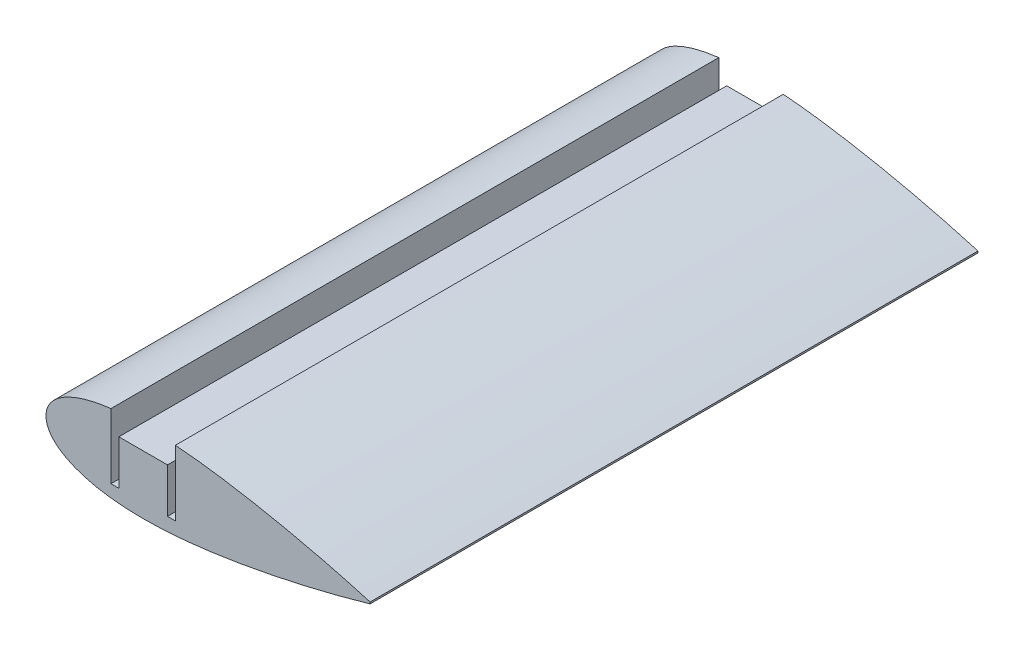
SolidWorks part; units mm, degrees
ref_plane "Спереди" through (0, 0, 0) normal (0, 0, 1) x (1, 0, 0)
ref_plane "Сверху" through (0, 0, 0) normal (0, 1, 0) x (1, 0, 0)
ref_plane "Справа" through (0, 0, 0) normal (1, 0, 0) x (0, 0, -1)
other "Configuration Table"
curve "Curve1"
  spline degree 3 poles (1, 0.0026, 0) (0.9995, 0.0028, 0) (0.9974, 0.0034, 0) (0.9928, 0.0047, 0) (0.9852, 0.0069, 0) (0.9746, 0.01, 0) (0.961, 0.0138, 0) (0.9446, 0.0183, 0) (0.9255, 0.0235, 0) (0.9037, 0.0292, 0) (0.8794, 0.0355, 0) (0.8529, 0.0421, 0) (0.8241, 0.0491, 0) (0.7933, 0.0562, 0) (0.7607, 0.0635, 0) (0.7266, 0.0709, 0) (0.691, 0.0782, 0) (0.6542, 0.0854, 0) (0.6165, 0.0923, 0) (0.5781, 0.0988, 0) (0.5392, 0.1049, 0) (0.5, 0.1104, 0) (0.4609, 0.1152, 0) (0.422, 0.1192, 0) (0.3836, 0.1222, 0) (0.3458, 0.1243, 0) (0.3091, 0.1252, 0) (0.2735, 0.1249, 0) (0.2392, 0.1234, 0) (0.2066, 0.1205, 0) (0.1758, 0.1164, 0) (0.147, 0.111, 0) (0.1203, 0.1043, 0) (0.096, 0.0965, 0) (0.0741, 0.0875, 0) (0.0549, 0.0774, 0) (0.0383, 0.0665, 0) (0.0245, 0.0546, 0) (0.0137, 0.042, 0) (0.0058, 0.0286, 0) (0.001, 0.0145, 0) (-0.0005, 0, 0) (0.001, -0.0145, 0) (0.0058, -0.0286, 0) (0.0137, -0.042, 0) (0.0245, -0.0546, 0) (0.0383, -0.0665, 0) (0.0549, -0.0774, 0) (0.0741, -0.0875, 0) (0.096, -0.0965, 0) (0.1203, -0.1043, 0) (0.147, -0.111, 0) (0.1758, -0.1164, 0) (0.2066, -0.1205, 0) (0.2392, -0.1234, 0) (0.2735, -0.1249, 0) (0.3091, -0.1252, 0) (0.3458, -0.1243, 0) (0.3836, -0.1222, 0) (0.422, -0.1192, 0) (0.4609, -0.1152, 0) (0.5, -0.1104, 0) (0.5392, -0.1049, 0) (0.5781, -0.0988, 0) (0.6165, -0.0923, 0) (0.6542, -0.0854, 0) (0.691, -0.0782, 0) (0.7266, -0.0709, 0) (0.7607, -0.0635, 0) (0.7933, -0.0562, 0) (0.8241, -0.0491, 0) (0.8529, -0.0421, 0) (0.8794, -0.0355, 0) (0.9037, -0.0292, 0) (0.9255, -0.0235, 0) (0.9446, -0.0183, 0) (0.961, -0.0138, 0) (0.9746, -0.01, 0) (0.9852, -0.0069, 0) (0.9928, -0.0047, 0) (0.9974, -0.0034, 0) (0.9995, -0.0028, 0) (1, -0.0026, 0) knots 0 0 0 0 0.000754 0.003013 0.006759 0.011967 0.018601 0.026614 0.035953 0.046555 0.058348 0.071256 0.085193 0.100071 0.115793 0.132259 0.149363 0.166997 0.185048 0.203403 0.221946 0.240561 0.259134 0.27755 0.295701 0.313483 0.330797 0.347552 0.363666 0.379065 0.393686 0.407475 0.420392 0.432406 0.443503 0.453686 0.462984 0.471456 0.479204 0.486388 0.493229 0.5 0.506771 0.513612 0.520796 0.528544 0.537016 0.546314 0.556497 0.567594 0.579608 0.592525 0.606314 0.620935 0.636334 0.652448 0.669203 0.686517 0.704299 0.72245 0.740866 0.759439 0.778054 0.796597 0.814952 0.833003 0.850637 0.867741 0.884207 0.899929 0.914807 0.928744 0.941652 0.953445 0.964047 0.973386 0.981399 0.988033 0.993241 0.996987 0.999246 1 1 1 1
sketch "Sketch2" plane through (0, 0, 0) normal (0, 0, 1) x (1, 0, 0)
  line L0 (55.999, 0.2099) -> (55.999, -0.2099) construction
  line L1 (55.999, 0) -> (-23.9777, 0) construction
  line L2 (-23.9777, 0) -> (-23.9777, 20.1567) construction
  line L3 (-7.5754, 10) -> (21.8908, 10) construction
  line L4 (55.999, 0.2099) -> (55.999, -0.2099)
  line L5 (0, 10) -> (0, -10) construction
  line L6 (55.999, -0.2099) -> (55.999, 14.9208) construction
  spline S1 degree 3 poles (55.999, 0.2099) (53.4639, 0.9505) (48.8039, 2.2339) (42.4289, 3.8199) (36.7434, 5.1209) (31.1997, 6.2872) (25.2824, 7.4075) (20.1765, 8.2452) (14.9796, 8.9749) (10.8215, 9.4486) (6.6974, 9.777) (3.6807, 9.9396) (0.7396, 10.0127) (-2.1078, 9.99) (-4.8439, 9.867) (-7.4522, 9.6409) (-9.9165, 9.3106) (-12.2218, 8.8772) (-14.354, 8.3437) (-16.3004, 7.7143) (-18.0494, 6.9954) (-19.5906, 6.1934) (-20.9154, 5.3156) (-22.0159, 4.3681) (-22.8849, 3.3565) (-23.5145, 2.285) (-23.8954, 1.1588) (-24.0187, 0) (-23.8954, -1.1588) (-23.5145, -2.285) (-22.8849, -3.3565) (-22.0159, -4.3681) (-20.9154, -5.3156) (-19.5906, -6.1934) (-18.0494, -6.9954) (-16.3004, -7.7143) (-14.354, -8.3437) (-12.2218, -8.8772) (-9.9165, -9.3106) (-7.4522, -9.6409) (-4.8439, -9.867) (-2.1078, -9.99) (0.7396, -10.0127) (3.6807, -9.9396) (7.7407, -9.7208) (12.9128, -9.2413) (19.1367, -8.4158) (25.2824, -7.4074) (31.1998, -6.2873) (37.5172, -4.9581) (44.7426, -3.2759) (51.0576, -1.6263) (54.945, -0.5178) (55.9579, -0.2219) (55.999, -0.2099) knots 0 0 0 0 0.046555 0.085193 0.115793 0.149363 0.185048 0.221946 0.240561 0.27755 0.295701 0.313483 0.330797 0.347552 0.363666 0.379065 0.393686 0.407475 0.420392 0.432406 0.443503 0.453686 0.462984 0.471456 0.479204 0.486388 0.493229 0.5 0.506771 0.513612 0.520796 0.528544 0.537016 0.546314 0.556497 0.567594 0.579608 0.592525 0.606314 0.620935 0.636334 0.652448 0.669203 0.686517 0.704299 0.740866 0.778054 0.814952 0.850637 0.884207 0.928744 0.981399 0.999246 1 1 1 1
  point P11 (0, 0)
  dimension "D1" = 20
extrude "Boss-Extrude1" add sketch "Sketch2" along normal blind 150
sketch "Sketch3" plane through (0, 0, 0) normal (0, 0, -1) x (-1, 0, 0)
  line L0 (6, -6.5) -> (7.95, -6.5)
  line L2 (-6, -6.5) -> (-6, 4.5)
  line L3 (-6, 4.5) -> (6, 4.5)
  line L4 (6, -6.5) -> (6, 4.5)
  line L5 (-6, -6.5) -> (6, 4.5) construction
  line L6 (-6, 4.5) -> (6, -6.5) construction
  line L7 (7.95, -6.5) -> (7.95, 9.5637)
  line L8 (-6, -6.5) -> (-7.95, -6.5)
  line L9 (-7.95, -6.5) -> (-7.95, 9.6738)
  line L10 (-11.2468, 10) -> (11.5184, 10) construction
  line L11 (0, 0) -> (0, 6.0357) construction
  line L12 (-7.95, -6.5) -> (7.95, -6.5) construction
  spline S0 degree 3 poles (275.2851, -1947.3186) (-351.5026, -245.2226) (-218.8463, -40.0718) (-42.4289, 3.8199) (-36.7434, 5.1209) (-31.1997, 6.2872) (-25.2824, 7.4075) (-20.1765, 8.2452) (-14.9796, 8.9749) (-10.8215, 9.4486) (-6.6974, 9.777) (-3.6807, 9.9396) (-0.7396, 10.0127) (2.1078, 9.99) (4.8439, 9.867) (7.4522, 9.6409) (9.9165, 9.3106) (12.2218, 8.8772) (14.354, 8.3437) (16.3004, 7.7143) (18.0494, 6.9954) (19.5906, 6.1934) (20.9154, 5.3156) (22.0159, 4.3681) (22.8849, 3.3565) (23.5145, 2.285) (23.8954, 1.1588) (24.0187, 0) (23.8954, -1.1588) (23.5145, -2.285) (22.8849, -3.3565) (22.0159, -4.3681) (20.9154, -5.3156) (19.5906, -6.1934) (18.0494, -6.9954) (16.3004, -7.7143) (14.354, -8.3437) (12.2218, -8.8772) (9.9165, -9.3106) (7.4522, -9.6409) (4.8439, -9.867) (2.1078, -9.99) (-0.7396, -10.0127) (-3.6807, -9.9396) (-7.7407, -9.7208) (-12.9128, -9.2413) (-19.1367, -8.4158) (-25.2824, -7.4074) (-31.1998, -6.2873) (-37.5172, -4.9581) (-44.7426, -3.2759) (-51.0576, -1.6263) (-78.1348, 6.0944) (-101.2564, 16.704) (-685.5525, -1897.6172) knots -3.088599 -3.088599 -3.088599 -3.088599 0.046555 0.085193 0.115793 0.149363 0.185048 0.221946 0.240561 0.27755 0.295701 0.313483 0.330797 0.347552 0.363666 0.379065 0.393686 0.407475 0.420392 0.432406 0.443503 0.453686 0.462984 0.471456 0.479204 0.486388 0.493229 0.5 0.506771 0.513612 0.520796 0.528544 0.537016 0.546314 0.556497 0.567594 0.579608 0.592525 0.606314 0.620935 0.636334 0.652448 0.669203 0.686517 0.704299 0.740866 0.778054 0.814952 0.850637 0.884207 0.928744 0.981399 0.999246 1.425061 1.425061 1.425061 1.425061 only from (-55.999, 0.2099) to (-55.999, -0.2099) construction
  spline S1 degree 3 poles (-7.95, 9.6738) (-7.5253, 9.7065) (-6.0943, 9.8095) (-3.6807, 9.9396) (-0.7396, 10.0127) (2.1078, 9.99) (4.8439, 9.867) (6.7781, 9.6993) (7.7981, 9.5819) (7.95, 9.5637) knots 0.288193 0.288193 0.288193 0.288193 0.295701 0.313483 0.330797 0.347552 0.363666 0.379065 0.381762 0.381762 0.381762 0.381762
  point P0 (0, -1)
  point P13 (-6.975, -6.5)
  dimension "D1" = 12
  dimension "D2" = 11
  dimension "D3" = 1.95
  dimension "D4" = 1.95
  dimension "D5" = 16.5
extrude "Cut-Extrude1" cut sketch "Sketch3" against normal up to next
